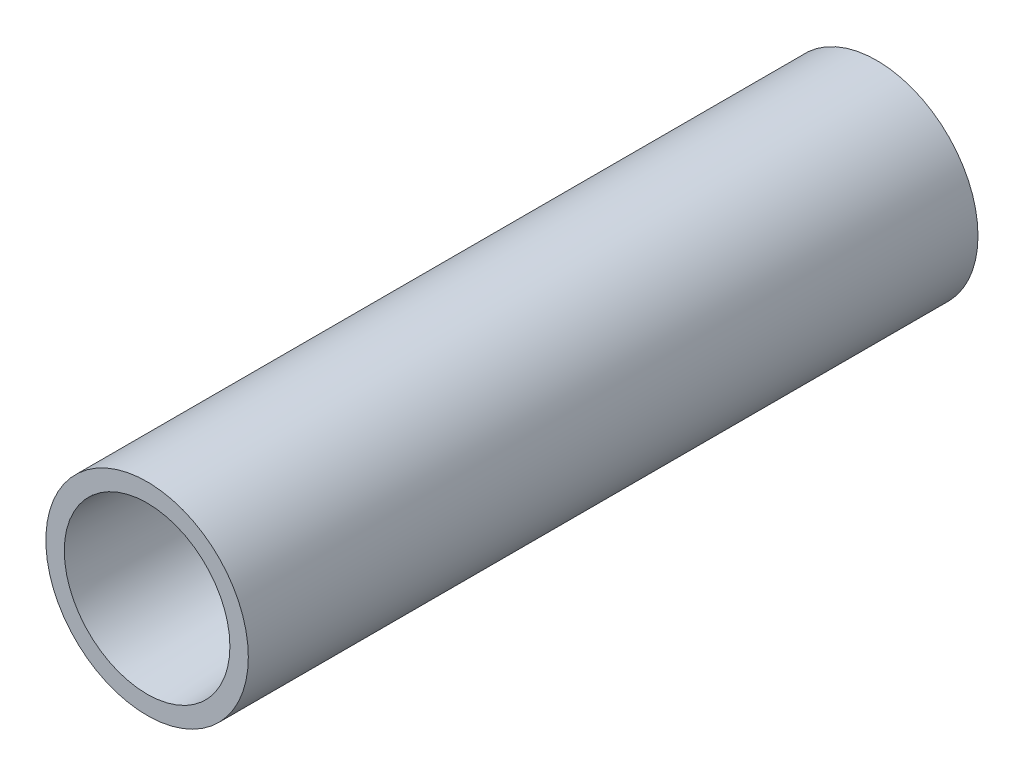
SolidWorks part; units mm, degrees
ref_plane "Front Plane" through (0, 0, 0) normal (0, 0, 1) x (1, 0, 0)
ref_plane "Top Plane" through (0, 0, 0) normal (0, 1, 0) x (1, 0, 0)
ref_plane "Right Plane" through (0, 0, 0) normal (1, 0, 0) x (0, 0, -1)
sketch "Sketch1" plane through (0, 0, 0) normal (0, 0, 1) x (1, 0, 0)
  circle A0 centre (0, 0) radius 2.775
  dimension "D1" = 5.55
extrude "Boss-Extrude1" add sketch "Sketch1" along normal blind 20
sketch "Sketch2" plane through (0, 0, 0) normal (0, 0, 1) x (1, 0, 0)
  circle A0 centre (0, 0) radius 2.27
  dimension "D1" = 4.54
extrude "Cut-Extrude1" cut sketch "Sketch2" along a picked direction on the side of the normal blind 5.68 draft 3.074
sketch "Sketch7" plane through (0, 0, 0) normal (0, 0, 1) x (1, 0, 0)
  circle A0 centre (0, 0) radius 1
extrude "Cut-Extrude2" cut sketch "Sketch7" along normal through all
sketch "Sketch9" plane through (0, 0, 20) normal (0, 0, 1) x (1, 0, 0)
  circle A0 centre (0, 0) radius 2.27
  circle A1 centre (0, 0) radius 2.27 construction
extrude "Cut-Extrude3" cut sketch "Sketch9" against normal blind 5.68 draft 3.074
